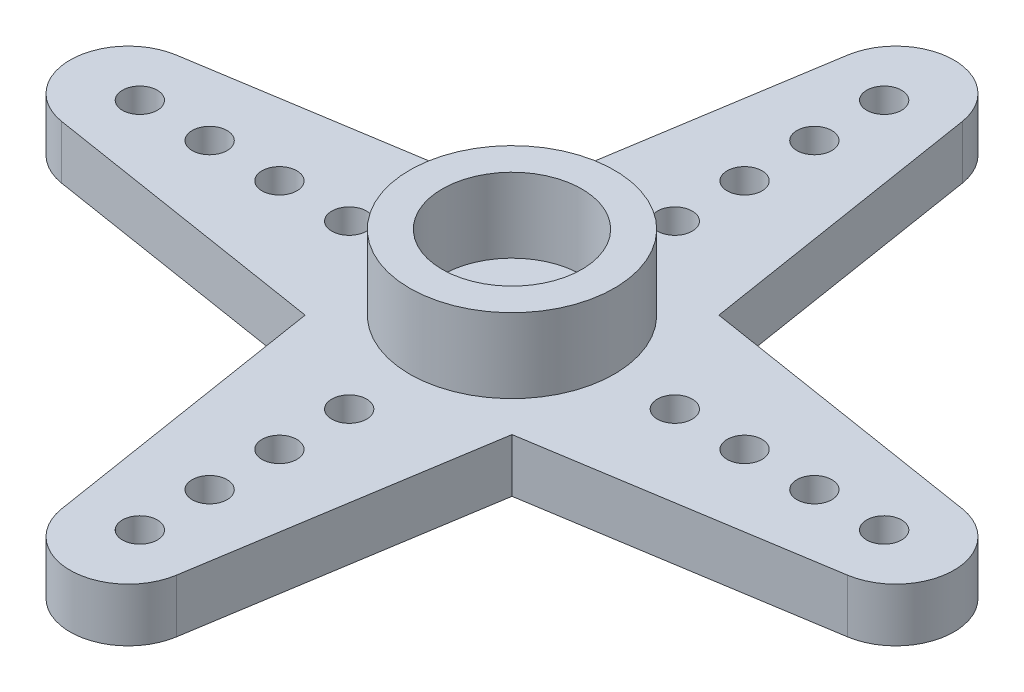
SolidWorks part; units mm, degrees
ref_plane "前视基准面" through (0, 0, 0) normal (0, 0, 1) x (1, 0, 0)
ref_plane "上视基准面" through (0, 0, 0) normal (0, 1, 0) x (1, 0, 0)
ref_plane "右视基准面" through (0, 0, 0) normal (1, 0, 0) x (0, 0, -1)
sketch "Sketch1" plane through (0, 0, 0) normal (0, 1, 0) x (1, 0, 0)
  circle A0 centre (0, 0) radius 6.1
  circle A1 centre (0, 0) radius 1.5
  dimension "D1" = 12.2
  dimension "D2" = 3
extrude "Boss-Extrude1" add sketch "Sketch1" along normal blind 2.3
sketch "Sketch2" plane through (0, 2.3, 0) normal (0, 1, 0) x (1, 0, 0)
  circle A0 centre (0, 0) radius 4.4
  circle A1 centre (0, 0) radius 3
  dimension "D1" = 8.8
  dimension "D2" = 6
extrude "Boss-Extrude2" add sketch "Sketch2" along normal blind 3.2
sketch "Sketch3" plane through (0, 0, 0) normal (0, -1, 0) x (1, 0, 0)
  line L0 (0, 0) -> (0, -19) construction
  line L1 (-2.469, -16.8925) -> (-4.5, -4.1183)
  line L2 (2.469, -16.8925) -> (4.5, -4.1183)
  arc A0 (-2.469, -16.8925) -> (2.469, -16.8925) centre (0, -16.5) ccw
  circle A1 centre (0, 0) radius 6.1 construction
  circle A2 centre (0, 0) radius 6.1
  circle A3 centre (0, -7) radius 0.75
  circle A4 centre (0, -10) radius 0.75
  circle A5 centre (0, -13) radius 0.75
  circle A6 centre (0, -16) radius 0.75
  circle A7 centre (0, 0) radius 1.5 construction
  point P12 (-6.1, 0)
  circle M3 centre (0, 0) radius 6.1
  dimension "D2" = 2.5
  dimension "D4" = 1.5
  dimension "D5" = 3
  dimension "D6" = 3
  dimension "D7" = 3
  dimension "D8" = 7
  dimension "D1" = 19
  dimension "D3" = 1.6
extrude "Boss-Extrude3" add sketch "Sketch3" against normal blind 2.3 contours A2 L0 A3 A4 A5 A6 A0 L2 | L0 L1 A0 A6 A5 A4 A3 M3
pattern_circular "CirPattern1" count 4 over 360 about axis through (0, 0, 0) along (0, 1, 0) of "Boss-Extrude3"
